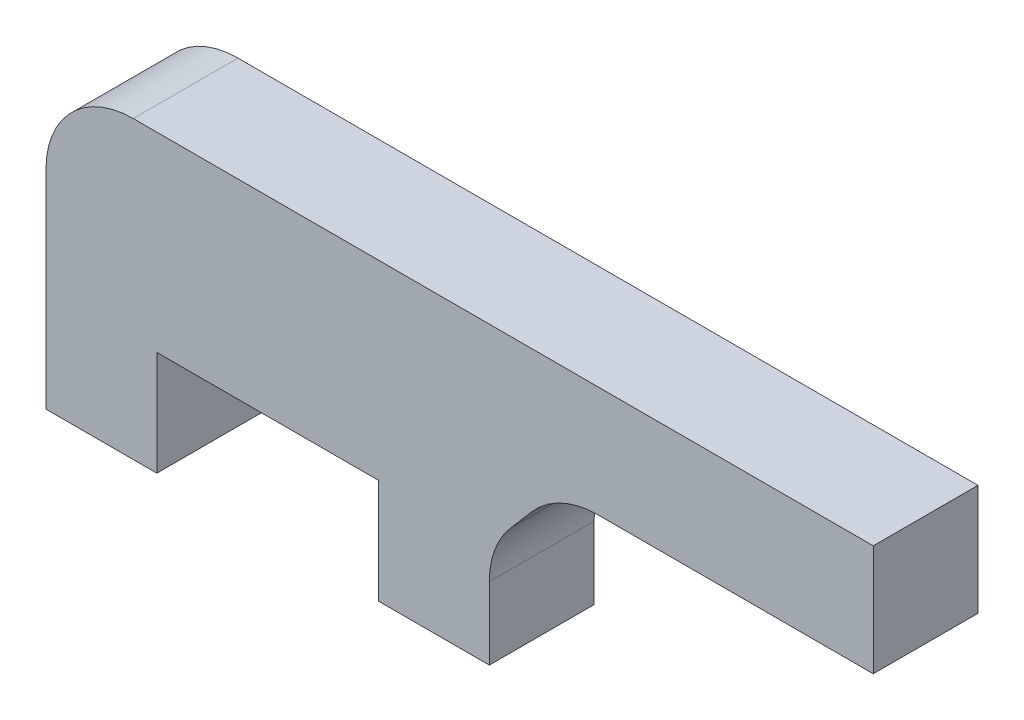
SolidWorks part; units mm, degrees
ref_plane "Front Plane" through (0, 0, 0) normal (0, 0, 1) x (1, 0, 0)
ref_plane "Top Plane" through (0, 0, 0) normal (0, 1, 0) x (1, 0, 0)
ref_plane "Right Plane" through (0, 0, 0) normal (1, 0, 0) x (0, 0, -1)
sketch "Sketch1" plane through (0, 0, 0) normal (0, 0, 1) x (1, 0, 0)
  line L0 (684.6898, 51.1944) -> (668.9191, 51.1944)
  line L4 (662.6898, 57.5444) -> (684.6898, 57.5444)
  line L5 (684.6898, 57.5444) -> (684.6898, 51.1944)
  line L7 (662.6898, 44.7641) -> (662.6898, 40.623)
  line L8 (662.6898, 57.5444) -> (642.2898, 57.5444)
  line L9 (637.2898, 52.5444) -> (637.2898, 40.623)
  line L12 (637.2898, 40.623) -> (643.6398, 40.623)
  line L14 (643.6398, 40.623) -> (643.6398, 46.6174)
  line L16 (663.8978, 48.023) -> (665.1271, 49.4534)
  line L17 (662.6898, 40.623) -> (656.3398, 40.623)
  line L18 (656.3398, 40.623) -> (656.3398, 46.6174)
  line L19 (656.3398, 46.6174) -> (643.6398, 46.6174)
  arc A0 (642.2898, 57.5444) -> (637.2898, 52.5444) centre (642.2898, 52.5444) ccw
  arc A1 (663.8978, 48.023) -> (662.6898, 44.7641) centre (667.6898, 44.7641) ccw
  arc A2 (665.1271, 49.4534) -> (668.9191, 51.1944) centre (668.9191, 46.1944) cw
  point P29 (662.6898, 46.6174)
  dimension "D1" = 5
  dimension "D2" = 5
  dimension "D3" = 5
extrude "Boss-Extrude1" add sketch "Sketch1" along normal blind 6 contours L4 L5 L0 A2 L16 A1 L7 L17 L18 L19 L14 L12 L9 A0 L8
